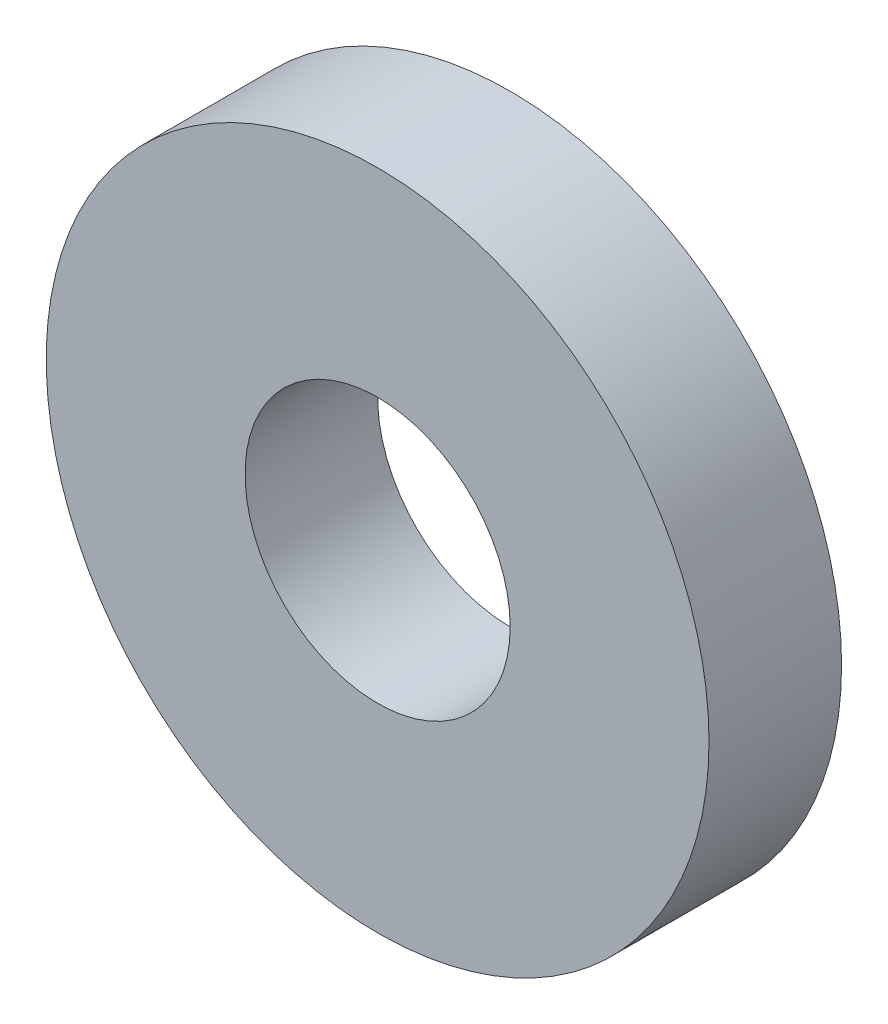
SolidWorks part; units mm, degrees
ref_plane "Front Plane" through (0, 0, 0) normal (0, 0, 1) x (1, 0, 0)
ref_plane "Top Plane" through (0, 0, 0) normal (0, 1, 0) x (1, 0, 0)
ref_plane "Right Plane" through (0, 0, 0) normal (1, 0, 0) x (0, 0, -1)
sketch "Sketch1" plane through (0, 0, 0) normal (0, 0, 1) x (1, 0, 0)
  circle A1 centre (0, 0) radius 12.5
  dimension "D2" = 25
extrude "Boss-Extrude3" add sketch "Sketch1" along normal blind 5 contours A1
sketch "Sketch5" plane through (0, 0, 5) normal (0, 0, 1) x (1, 0, 0)
  circle A0 centre (0, 0) radius 5
extrude "Cut-Extrude1" cut sketch "Sketch5" against normal through all
